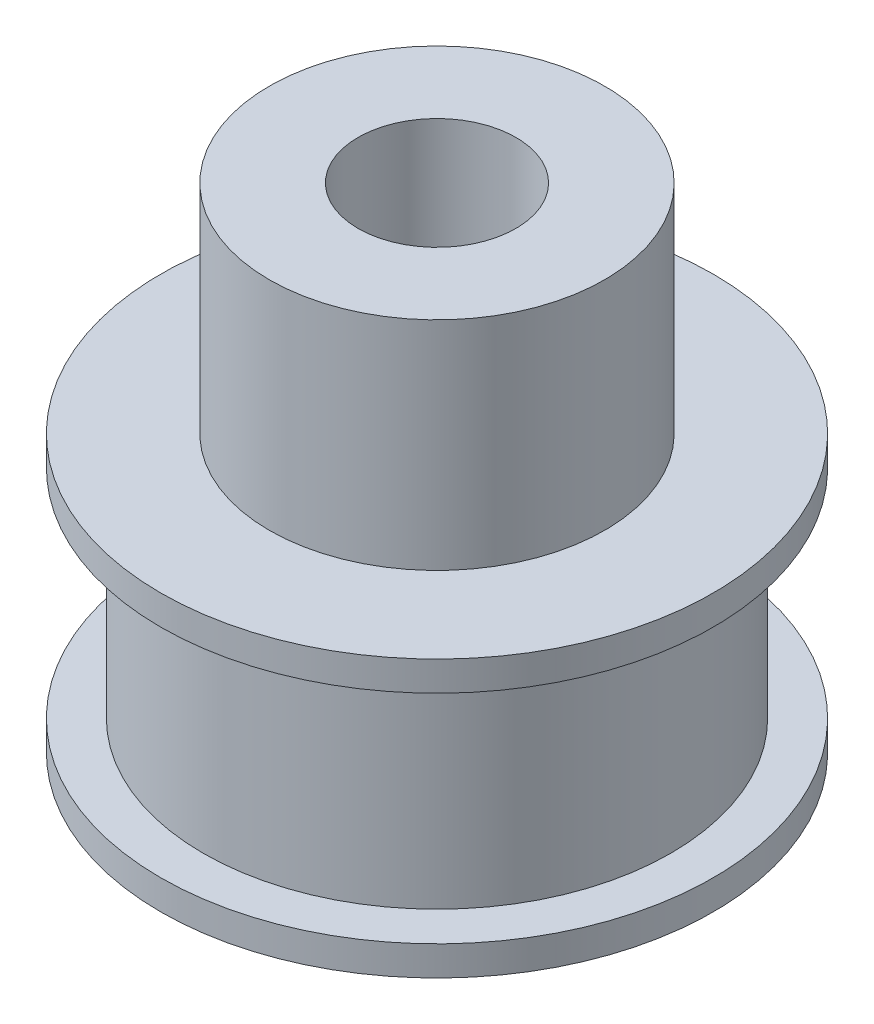
SolidWorks part; units mm, degrees
ref_plane "Front Plane" through (0, 0, 0) normal (0, 0, 1) x (1, 0, 0)
ref_plane "Top Plane" through (0, 0, 0) normal (0, 1, 0) x (1, 0, 0)
ref_plane "Right Plane" through (0, 0, 0) normal (1, 0, 0) x (0, 0, -1)
sketch "Sketch1" plane through (0, 0, 0) normal (0, 1, 0) x (1, 0, 0)
  circle A0 centre (0, 0) radius 14
  dimension "D1" = 28
extrude "Boss-Extrude1" add sketch "Sketch1" along normal blind 1.5
sketch "Sketch2" plane through (0, 1.5, 0) normal (0, 1, 0) x (1, 0, 0)
  circle A0 centre (0, 0) radius 11.85
  dimension "D1" = 23.7
extrude "Boss-Extrude2" add sketch "Sketch2" along normal blind 11
sketch "Sketch3" plane through (0, 12.5, 0) normal (0, 1, 0) x (1, 0, 0)
  circle A0 centre (0, 0) radius 14
  dimension "D1" = 28
extrude "Boss-Extrude3" add sketch "Sketch3" along normal blind 1.5
sketch "Sketch4" plane through (0, 14, 0) normal (0, 1, 0) x (1, 0, 0)
  circle A0 centre (0, 0) radius 8.5
  dimension "D1" = 17
extrude "Boss-Extrude4" add sketch "Sketch4" along normal blind 11
sketch "Sketch5" plane through (0, 25, 0) normal (0, 1, 0) x (1, 0, 0)
  circle A0 centre (0, 0) radius 4
  dimension "D1" = 8
extrude "Cut-Extrude1" cut sketch "Sketch5" against normal through all
